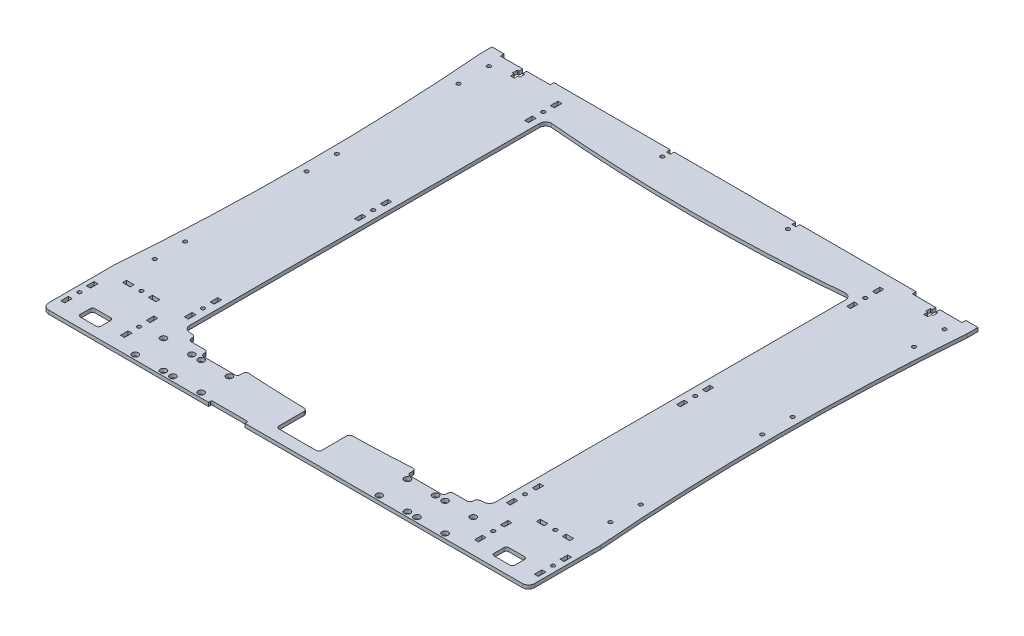
SolidWorks part; units mm, degrees
ref_plane "Alzado" through (0, 0, 0) normal (0, 0, 1) x (1, 0, 0)
ref_plane "Planta" through (0, 0, 0) normal (0, 1, 0) x (1, 0, 0)
ref_plane "Vista lateral" through (0, 0, 0) normal (1, 0, 0) x (0, 0, -1)
sketch "Croquis1" plane through (0, 0, 0) normal (0, 1, 0) x (1, 0, 0)
  line L0 (200, 370) -> (200, 0) construction
  line L1 (0, 0) -> (400, 0)
  line L2 (0, 0) -> (0, 370)
  line L3 (0, 370) -> (10, 370)
  line L4 (400, 0) -> (400, 370)
  line L5 (52.7, 17.8) -> (55.9, 17.8)
  line L6 (3.5, 17.8) -> (6.7, 17.8)
  line L7 (3.5, 17.8) -> (3.5, 11.6)
  line L8 (3.5, 11.6) -> (6.7, 11.6)
  line L9 (6.7, 17.8) -> (6.7, 11.6)
  line L10 (3.5, 39) -> (6.7, 39)
  line L11 (3.5, 39) -> (3.5, 32.8)
  line L12 (3.5, 32.8) -> (6.7, 32.8)
  line L13 (6.7, 39) -> (6.7, 32.8)
  line L14 (52.7, 17.8) -> (52.7, 11.6)
  line L15 (52.7, 11.6) -> (55.9, 11.6)
  line L16 (55.9, 17.8) -> (55.9, 11.6)
  line L17 (52.7, 39) -> (55.9, 39)
  line L18 (52.7, 39) -> (52.7, 32.8)
  line L19 (52.7, 32.8) -> (55.9, 32.8)
  line L20 (55.9, 39) -> (55.9, 32.8)
  line L21 (69.1, 218.4) -> (69.1, 212.2)
  line L22 (16, 53.2) -> (22.2, 53.2)
  line L23 (16, 53.2) -> (16, 50)
  line L24 (16, 50) -> (22.2, 50)
  line L25 (22.2, 53.2) -> (22.2, 50)
  line L26 (37.2, 53.2) -> (43.4, 53.2)
  line L27 (37.2, 53.2) -> (37.2, 50)
  line L28 (37.2, 50) -> (43.4, 50)
  line L29 (43.4, 53.2) -> (43.4, 50)
  line L30 (65.9, 57.2) -> (69.1, 57.2)
  line L31 (65.9, 57.2) -> (65.9, 51)
  line L32 (65.9, 51) -> (69.1, 51)
  line L33 (69.1, 57.2) -> (69.1, 51)
  line L34 (65.9, 78.4) -> (69.1, 78.4)
  line L35 (65.9, 78.4) -> (65.9, 72.2)
  line L36 (65.9, 72.2) -> (69.1, 72.2)
  line L37 (69.1, 78.4) -> (69.1, 72.2)
  line L38 (65.9, 218.4) -> (69.1, 218.4)
  line L39 (65.9, 218.4) -> (65.9, 212.2)
  line L40 (65.9, 212.2) -> (69.1, 212.2)
  line L41 (65.9, 197.2) -> (69.1, 197.2)
  line L42 (69.1, 197.2) -> (69.1, 191)
  line L43 (65.9, 197.2) -> (65.9, 191)
  line L44 (65.9, 191) -> (69.1, 191)
  line L45 (69.1, 78.4) -> (69.1, 218.4) construction
  line L46 (69.1, 337.2) -> (69.1, 331)
  line L47 (65.9, 337.2) -> (69.1, 337.2)
  line L48 (65.9, 337.2) -> (65.9, 331)
  line L49 (65.9, 331) -> (69.1, 331)
  line L50 (65.9, 352.2) -> (69.1, 352.2)
  line L51 (69.1, 358.4) -> (69.1, 352.2)
  line L52 (65.9, 358.4) -> (69.1, 358.4)
  line L53 (65.9, 358.4) -> (65.9, 352.2)
  line L54 (69.1, 197.2) -> (69.1, 337.2) construction
  line L55 (330.9, 197.2) -> (330.9, 337.2) construction
  line L56 (330.9, 78.4) -> (330.9, 218.4) construction
  line L57 (334.1, 358.4) -> (334.1, 352.2)
  line L58 (334.1, 358.4) -> (330.9, 358.4)
  line L59 (330.9, 358.4) -> (330.9, 352.2)
  line L60 (334.1, 352.2) -> (330.9, 352.2)
  line L61 (334.1, 331) -> (330.9, 331)
  line L62 (334.1, 337.2) -> (334.1, 331)
  line L63 (334.1, 337.2) -> (330.9, 337.2)
  line L64 (330.9, 337.2) -> (330.9, 331)
  line L65 (334.1, 191) -> (330.9, 191)
  line L66 (334.1, 197.2) -> (334.1, 191)
  line L67 (330.9, 197.2) -> (330.9, 191)
  line L68 (334.1, 197.2) -> (330.9, 197.2)
  line L69 (334.1, 212.2) -> (330.9, 212.2)
  line L70 (334.1, 218.4) -> (334.1, 212.2)
  line L71 (334.1, 218.4) -> (330.9, 218.4)
  line L72 (330.9, 78.4) -> (330.9, 72.2)
  line L73 (334.1, 72.2) -> (330.9, 72.2)
  line L74 (334.1, 78.4) -> (334.1, 72.2)
  line L75 (334.1, 78.4) -> (330.9, 78.4)
  line L76 (330.9, 57.2) -> (330.9, 51)
  line L77 (334.1, 51) -> (330.9, 51)
  line L78 (334.1, 57.2) -> (334.1, 51)
  line L79 (334.1, 57.2) -> (330.9, 57.2)
  line L80 (356.6, 53.2) -> (356.6, 50)
  line L81 (362.8, 50) -> (356.6, 50)
  line L82 (362.8, 53.2) -> (362.8, 50)
  line L83 (362.8, 53.2) -> (356.6, 53.2)
  line L84 (377.8, 53.2) -> (377.8, 50)
  line L85 (384, 50) -> (377.8, 50)
  line L86 (384, 53.2) -> (384, 50)
  line L87 (384, 53.2) -> (377.8, 53.2)
  line L88 (330.9, 218.4) -> (330.9, 212.2)
  line L89 (344.1, 39) -> (344.1, 32.8)
  line L90 (347.3, 32.8) -> (344.1, 32.8)
  line L91 (347.3, 39) -> (347.3, 32.8)
  line L92 (347.3, 39) -> (344.1, 39)
  line L93 (344.1, 17.8) -> (344.1, 11.6)
  line L94 (347.3, 11.6) -> (344.1, 11.6)
  line L95 (347.3, 17.8) -> (347.3, 11.6)
  line L96 (393.3, 39) -> (393.3, 32.8)
  line L97 (396.5, 32.8) -> (393.3, 32.8)
  line L98 (396.5, 39) -> (396.5, 32.8)
  line L99 (396.5, 39) -> (393.3, 39)
  line L100 (393.3, 17.8) -> (393.3, 11.6)
  line L101 (396.5, 11.6) -> (393.3, 11.6)
  line L102 (396.5, 17.8) -> (396.5, 11.6)
  line L103 (396.5, 17.8) -> (393.3, 17.8)
  line L104 (347.3, 17.8) -> (344.1, 17.8)
  line L105 (400, 0) -> (400, 370)
  line L106 (51, 370) -> (146.7, 370)
  line L108 (10, 370) -> (10, 366.9)
  line L109 (10, 366.9) -> (28.4, 366.9)
  line L110 (51, 370) -> (51, 366.9)
  line L111 (31.6, 366.9) -> (51, 366.9)
  line L113 (28.4, 366.9) -> (28.4, 363.9)
  line L114 (28.4, 356.9) -> (31.6, 356.9)
  line L115 (31.6, 366.9) -> (31.6, 363.9)
  line L116 (27, 363.9) -> (28.4, 363.9)
  line L117 (27, 363.9) -> (27, 359.9)
  line L118 (27, 359.9) -> (28.4, 359.9)
  line L119 (33, 363.9) -> (33, 359.9)
  line L120 (31.6, 363.9) -> (33, 363.9)
  line L121 (31.6, 359.9) -> (31.6, 356.9)
  line L122 (28.4, 359.9) -> (28.4, 356.9)
  line L123 (31.6, 359.9) -> (33, 359.9)
  line L124 (349, 370) -> (349, 366.9)
  line L125 (368.4, 366.9) -> (349, 366.9)
  line L126 (368.4, 366.9) -> (368.4, 363.9)
  line L127 (368.4, 363.9) -> (367, 363.9)
  line L128 (367, 363.9) -> (367, 359.9)
  line L129 (368.4, 359.9) -> (367, 359.9)
  line L130 (368.4, 359.9) -> (368.4, 356.9)
  line L131 (371.6, 356.9) -> (368.4, 356.9)
  line L132 (371.6, 359.9) -> (371.6, 356.9)
  line L133 (373, 359.9) -> (371.6, 359.9)
  line L134 (373, 363.9) -> (373, 359.9)
  line L135 (373, 363.9) -> (371.6, 363.9)
  line L136 (371.6, 366.9) -> (371.6, 363.9)
  line L137 (390, 366.9) -> (371.6, 366.9)
  line L138 (390, 370) -> (390, 366.9)
  line L139 (390, 370) -> (400, 370)
  line L140 (69.1, 51) -> (69.1, 0) construction
  line L141 (99.1, 31) -> (69.1, 0) construction
  line L142 (69.1, 0) -> (99.1, 0)
  line L143 (69.1, 0) -> (69.1, 31) construction
  line L144 (69.1, 31) -> (99.1, 31) construction
  line L145 (99.1, 0) -> (99.1, 31) construction
  line L146 (99.6, 0) -> (99.6, 37.4867) construction
  line L147 (72.5, 3.9) -> (95.7, 3.9) construction
  line L148 (72.5, 3.9) -> (72.5, 27.1) construction
  line L149 (72.5, 27.1) -> (95.7, 27.1) construction
  line L150 (95.7, 3.9) -> (95.7, 27.1) construction
  line L151 (72.5, 3.9) -> (95.7, 27.1) construction
  line L152 (72.5, 27.1) -> (95.7, 3.9) construction
  line L153 (150, 370) -> (250, 370)
  line L155 (146.7, 370) -> (146.7, 366.9)
  line L156 (146.7, 366.9) -> (150, 366.9)
  line L157 (150, 370) -> (150, 366.9)
  line L158 (148.35, 366.9) -> (148.35, 357.7293) construction
  line L159 (253.3, 370) -> (253.3, 366.9)
  line L160 (253.3, 366.9) -> (250, 366.9)
  line L161 (250, 370) -> (250, 366.9)
  line L162 (253.3, 370) -> (349, 370)
  line L163 (12.5, 366.9) -> (12.5, 0) construction
  circle A0 centre (5.1, 25.3) radius 1.55
  circle A1 centre (54.3, 25.3) radius 1.55
  circle A2 centre (67.5, 64.7) radius 1.55
  circle A3 centre (67.5, 204.7) radius 1.55
  circle A4 centre (67.5, 344.7) radius 1.55
  circle A5 centre (332.5, 344.7) radius 1.55
  circle A6 centre (332.5, 204.7) radius 1.55
  circle A7 centre (332.5, 64.7) radius 1.55
  circle A8 centre (345.7, 25.3) radius 1.55
  circle A9 centre (394.9, 25.3) radius 1.55
  circle A10 centre (29.7, 51.8) radius 1.55
  circle A11 centre (370.3, 51.8) radius 1.55
  circle A12 centre (72.5, 27.1) radius 2.55
  circle A13 centre (95.7, 27.1) radius 2.55
  circle A14 centre (72.5, 3.9) radius 2.55
  circle A15 centre (95.7, 3.9) radius 2.55
  circle A16 centre (327.5, 27.1) radius 2.55
  circle A17 centre (327.5, 3.9) radius 2.55
  circle A18 centre (304.3, 3.9) radius 2.55
  circle A19 centre (304.3, 27.1) radius 2.55
  circle A28 centre (103.5, 3.9) radius 2.55
  circle A29 centre (126.7, 3.9) radius 2.55
  circle A30 centre (126.7, 27.1) radius 2.55
  circle A31 centre (103.5, 27.1) radius 2.55
  circle A32 centre (273.3, 3.9) radius 2.55
  circle A33 centre (296.5, 3.9) radius 2.55
  circle A34 centre (296.5, 27.1) radius 2.55
  circle A35 centre (273.3, 27.1) radius 2.55
  circle A36 centre (148.35, 361.9) radius 1.55
  circle A37 centre (251.65, 361.9) radius 1.55
  circle A38 centre (12.5, 354.9) radius 1.55
  circle A39 centre (12.5, 329.9) radius 1.55
  circle A40 centre (12.5, 304.9) radius 1.55 [skipped]
  circle A41 centre (12.5, 279.9) radius 1.55 [skipped]
  circle A42 centre (12.5, 254.9) radius 1.55 [skipped]
  circle A43 centre (12.5, 229.9) radius 1.55
  circle A44 centre (12.5, 204.9) radius 1.55
  circle A45 centre (12.5, 179.9) radius 1.55 [skipped]
  circle A46 centre (12.5, 154.9) radius 1.55 [skipped]
  circle A48 centre (12.5, 104.9) radius 1.55
  circle A49 centre (12.5, 79.9) radius 1.55
  circle A50 centre (12.5, 129.9) radius 1.55 [skipped]
  circle A51 centre (387.5, 79.9) radius 1.55
  circle A52 centre (387.5, 104.9) radius 1.55
  circle A53 centre (387.5, 204.9) radius 1.55
  circle A54 centre (387.5, 229.9) radius 1.55
  circle A55 centre (387.5, 329.9) radius 1.55
  circle A56 centre (387.5, 354.9) radius 1.55
  point P43 (69.1, 54.1)
  point P168 (84.1, 15.5)
  point P219 (12.5, 66.9)
  dimension "D11" = 3.1
  dimension "D14" = 2
  dimension "D32" = 3.1
  dimension "D34" = 67.5
  dimension "D39" = 3.1
  dimension "D40" = 7.5
  dimension "D56" = 5.1
  dimension "D57" = 0.5
  dimension "D58" = 3.3
  dimension "D61" = 3.1
  dimension "D62" = 5
  dimension "D63" = 12.5
  dimension "D64" = 3.1
  dimension "D68" = 25
  dimension "D1" = 370
  dimension "D2" = 400
  dimension "D3" = 3.2
  dimension "D4" = 6.2
  dimension "D5" = 6.2
  dimension "D6" = 3.2
  dimension "D7" = 3.5
  dimension "D8" = 11.6
  dimension "D9" = 15
  dimension "D10" = 3.5
  dimension "D12" = 7.5
  dimension "D13" = 5.1
  dimension "D15" = 46
  dimension "D16" = 6.2
  dimension "D17" = 6.2
  dimension "D18" = 3.2
  dimension "D19" = 3.2
  dimension "D20" = 15
  dimension "D21" = 16
  dimension "D22" = 50
  dimension "D23" = 50
  dimension "D24" = 3.2
  dimension "D25" = 6.2
  dimension "D26" = 6.2
  dimension "D27" = 3.2
  dimension "D28" = 65.9
  dimension "D29" = 65.9
  dimension "D30" = 15
  dimension "D31" = 51
  dimension "D33" = 7.5
  dimension "D36" = 140
  dimension "D38" = 140
  dimension "D41" = 1.4
  dimension "D42" = 3.1
  dimension "D43" = 10
  dimension "D44" = 41
  dimension "D45" = 3.2
  dimension "D46" = 10
  dimension "D47" = 4
  dimension "D48" = 6
  dimension "D49" = 1.4
  dimension "D50" = 3
  dimension "D51" = 18.4
  dimension "D52" = 30
  dimension "D53" = 31
  dimension "D54" = 23.2
  dimension "D55" = 23.2
  dimension "D59" = 3.1
  dimension "D60" = 50
  dimension "D65" = 12
  dimension "D66" = 300
  dimension "D35" = 2
  dimension "D37" = 2
  dimension "D67" = 12
extrude "Saliente-Extruir1" add sketch "Croquis1" along normal blind 3 contours L1 L4 L3 L2 A8 A6 L57 L60 L59 L58 L34 L37 L36 L35 L30 L33 L32 L31 L26 L29 L28 L27 L22 L25 L24 L23 L17 L20 L19 L18 L5 L16 L15 L14 L10 L13 L12 L11 L6 L9
sketch "Croquis2" plane through (0, 3, 0) normal (0, 1, 0) x (1, 0, 0)
  line L0 (51, 370) -> (146.7, 370) construction
  line L1 (79.1, 340) -> (320.9, 340) construction
  line L2 (74.1, 335) -> (74.1, 47.1)
  line L3 (79.1, 42.1) -> (320.9, 42.1) construction
  line L4 (325.9, 335) -> (325.9, 47.1)
  line L5 (69.1, 337.2) -> (69.1, 331) construction
  line L6 (330.9, 337.2) -> (330.9, 331) construction
  circle A0 centre (273.3, 27.1) radius 2.55 construction
  arc A1 (325.9, 47.1) -> (320.9, 42.1) centre (320.9, 47.1) cw
  arc A2 (79.1, 340) -> (320.9, 340) centre (200, 1685.3457) ccw
  arc A3 (74.1, 335) -> (79.1, 340) centre (79.1, 335) cw
  arc A4 (320.9, 340) -> (325.9, 335) centre (320.9, 335) cw
  arc A5 (79.1, 42.1) -> (74.1, 47.1) centre (79.1, 47.1) cw
  arc A6 (79.1, 42.1) -> (320.9, 42.1) centre (200, 1082.7326) ccw
  dimension "D5" = 5
  dimension "D6" = 5
  dimension "D1" = 30
  dimension "D2" = 5
  dimension "D3" = 5
  dimension "D4" = 15
extrude "Cortar-Extruir1" cut sketch "Croquis2" against normal up to surface (3 mm away) up to face at (387.5, 0, -328.35)
fillet "Redondeo1" radius 5 2 edges at (400, 1.5, 0) (0, 1.5, 0)
sketch "Croquis4" plane through (0, 3, 0) normal (0, 1, 0) x (1, 0, 0)
  line L0 (0, 5) -> (0, 370) construction
  line L1 (0, 361) -> (6, 361) construction
  line L2 (0, 361) -> (0, 59.2)
  line L3 (0, 59.2) -> (6, 59.2) construction
  line L4 (6, 361) -> (6, 59.2) construction
  line L5 (0, 367) -> (18.0662, 367) construction
  line L6 (5, 53.2) -> (0, 53.2) construction
  line L7 (200, 370) -> (200, 0) construction
  line L9 (150, 370) -> (250, 370) construction
  line L12 (5, 0) -> (395, 0) construction
  line L13 (400, 361) -> (400, 59.2)
  arc A0 (0, 361) -> (0, 59.2) centre (-1894.5675, 210.1) cw
  arc A2 (0, 361) -> (0, 59.2) centre (1894.5675, 210.1) ccw
  arc A3 (400, 361) -> (400, 59.2) centre (2294.5675, 210.1) ccw
  dimension "D1" = 6
  dimension "D2" = 6
  dimension "D3" = 6
extrude "Cortar-Extruir3" cut sketch "Croquis4" against normal up to surface (3 mm away) contours A0 L2 | L13 A3 up to face at (200, 0, -189.4974)
sketch "Croquis5" plane through (0, 3, 0) normal (0, 1, 0) x (1, 0, 0)
  line L0 (100.1, 29.335) -> (100.1, 41.5) construction
  line L5 (130.1, 28.5) -> (130.1, 47.9346) construction
  line L7 (200, 0) -> (200, 92.2455) construction
  line L8 (100.1, 30.5) -> (130.1, 30.5)
  line L9 (100.1, 30.5) -> (100.1, 41.5)
  line L10 (100.1, 41.5) -> (130.1, 41.5)
  line L11 (130.1, 30.5) -> (130.1, 41.5)
  line L12 (5, 0) -> (395, 0) construction
  line L13 (299.9, 30.5) -> (299.9, 41.5)
  line L14 (299.9, 30.5) -> (269.9, 30.5)
  line L15 (299.9, 41.5) -> (269.9, 41.5)
  line L16 (269.9, 30.5) -> (269.9, 41.5)
  line L17 (6.7, 17.8) -> (6.7, 11.6) construction
  line L18 (182.5, 35.2467) -> (217.5, 35.2467)
  line L19 (182.5, 35.2467) -> (182.5, 10)
  line L20 (182.5, 10) -> (217.5, 10)
  line L21 (217.5, 35.2467) -> (217.5, 10)
  line L22 (23.2, 20) -> (36.2, 20)
  line L23 (21.2, 18) -> (21.2, 10)
  line L24 (23.2, 8) -> (36.2, 8)
  line L25 (38.2, 18) -> (38.2, 10)
  line L27 (378.8, 18) -> (378.8, 10)
  line L28 (376.8, 8) -> (363.8, 8)
  line L29 (361.8, 18) -> (361.8, 10)
  line L30 (376.8, 20) -> (363.8, 20)
  arc A0 (79.1, 42.1) -> (320.9, 42.1) centre (200, 1082.7326) ccw construction
  arc A1 (23.2, 20) -> (21.2, 18) centre (23.2, 18) ccw
  arc A2 (38.2, 18) -> (36.2, 20) centre (36.2, 18) ccw
  arc A3 (36.2, 8) -> (38.2, 10) centre (36.2, 10) ccw
  arc A4 (23.2, 8) -> (21.2, 10) centre (23.2, 10) cw
  arc A5 (376.8, 20) -> (378.8, 18) centre (376.8, 18) cw
  arc A6 (376.8, 8) -> (378.8, 10) centre (376.8, 10) ccw
  arc A7 (363.8, 8) -> (361.8, 10) centre (363.8, 10) cw
  arc A8 (361.8, 18) -> (363.8, 20) centre (363.8, 18) cw
  circle A9 centre (103.5, 27.1) radius 2.55 construction
  point P36 (21.2, 20)
  point P37 (38.2, 20)
  point P40 (38.2, 8)
  dimension "D9" = 2
  dimension "D1" = 11
  dimension "D2" = 10
  dimension "D3" = 35
  dimension "D4" = 17.5
  dimension "D5" = 17
  dimension "D6" = 12
  dimension "D7" = 8
  dimension "D8" = 14.5
  dimension "D10" = 3.4
  dimension "D11" = 3.4
  dimension "D12" = 2.235
extrude "Cortar-Extruir4" cut sketch "Croquis5" against normal up to surface (3 mm away) up to face at (387.5, 0, -353.35)
fillet "Redondeo2" radius 2 6 edges at (299.9, 1.5, -30.5) (269.9, 1.5, -30.5) (100.1, 1.5, -30.5) (130.1, 1.5, -30.5) (217.5, 1.5, -10) (182.5, 1.5, -10)
sketch "Croquis6" plane through (0, 3, 0) normal (0, 1, 0) x (1, 0, 0)
  line L0 (5, 0) -> (395, 0) construction
  line L1 (136.7, 0) -> (166.7, 0)
  line L2 (136.7, 0) -> (136.7, 1.5)
  line L3 (137.7, 2.5) -> (165.7, 2.5)
  line L4 (166.7, 0) -> (166.7, 1.5)
  circle A0 centre (126.7, 3.9) radius 2.55 construction
  arc A1 (136.7, 1.5) -> (137.7, 2.5) centre (137.7, 1.5) cw
  arc A2 (165.7, 2.5) -> (166.7, 1.5) centre (165.7, 1.5) cw
  point P10 (136.7, 2.5)
  point P13 (166.7, 2.5)
  dimension "D4" = 1
  dimension "D1" = 30
  dimension "D2" = 2.5
  dimension "D3" = 10
extrude "Cortar-Extruir5" cut sketch "Croquis6" against normal up to surface (3 mm away) up to face at (200, 0, -78.494)
sketch "Croquis7" plane through (0, 3, 0) normal (0, 1, 0) x (1, 0, 0)
  line L0 (200, 370) -> (200, 0) construction
  line L1 (150, 370) -> (250, 370) construction
  line L2 (166.7, 0) -> (395, 0) construction
  line L3 (100.1, 39.8745) -> (100.1, 32.5) construction
  line L4 (100.1, 36.0313) -> (84.1, 36.0313)
  line L5 (100.1, 36.0313) -> (100.1, 41.5313)
  line L6 (100.1, 41.5313) -> (84.1, 41.5313)
  line L7 (84.1, 36.0313) -> (84.1, 41.5313)
  line L8 (299.9, 41.5313) -> (315.9, 41.5313)
  line L9 (315.9, 36.0313) -> (315.9, 41.5313)
  line L10 (299.9, 36.0313) -> (299.9, 41.5313)
  line L11 (299.9, 36.0313) -> (315.9, 36.0313)
  arc A1 (79.1, 42.1) -> (100.1, 39.8745) centre (200, 1082.7326) ccw construction
  dimension "D1" = 5.5
  dimension "D3" = 16
extrude "Cortar-Extruir6" cut sketch "Croquis7" against normal up to surface (3 mm away) up to face at (200, 0, -78.494)
fillet "Redondeo3" radius 2.5 10 edges at (269.9, 1.5, -37.435) (315.9, 1.5, -41.5313) (299.9, 1.5, -36.0313) (217.5, 1.5, -35.2467) (182.5, 1.5, -35.2467) (130.1, 1.5, -37.435) (100.1, 1.5, -36.0313) (84.1, 1.5, -41.5313) (315.9, 1.5, -36.0313) (84.1, 1.5, -36.0313)
